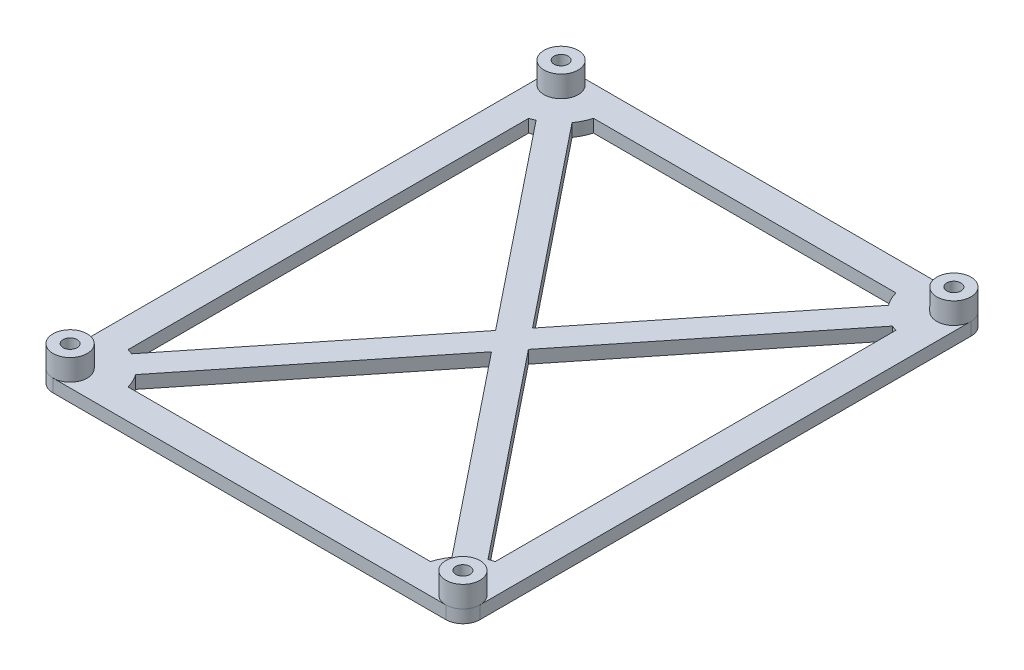
SolidWorks part; units mm, degrees
ref_plane "Front Plane" through (0, 0, 0) normal (0, 0, 1) x (1, 0, 0)
ref_plane "Top Plane" through (0, 0, 0) normal (0, 1, 0) x (1, 0, 0)
ref_plane "Right Plane" through (0, 0, 0) normal (1, 0, 0) x (0, 0, -1)
sketch "Sketch1" plane through (0, 0, 0) normal (0, 1, 0) x (1, 0, 0)
  line L1 (50, 61.5) -> (-50, 61.5)
  line L2 (50, 61.5) -> (50, -61.5)
  line L3 (50, -61.5) -> (-50, -61.5)
  line L4 (-50, 61.5) -> (-50, -61.5)
  line L5 (0, -61.5) -> (0, 61.5) construction
  line L6 (50, 0) -> (-50, 0) construction
  point P0 (0, 0)
  dimension "D1" = 123
  dimension "D2" = 100
extrude "Boss-Extrude1" add sketch "Sketch1" along normal blind 3
sketch "Sketch2" plane through (0, 3, 0) normal (0, 1, 0) x (1, 0, 0)
  line L0 (-46, 0) -> (0, 0) construction
  line L1 (-46, 57.5) -> (46, 57.5) construction
  line L2 (-46, 57.5) -> (-46, -57.5) construction
  line L3 (-46, -57.5) -> (46, -57.5) construction
  line L4 (46, 57.5) -> (46, -57.5) construction
  line L5 (0, 0) -> (0, 57.5) construction
  circle A1 centre (46, 57.5) radius 4
  circle A2 centre (46, -57.5) radius 4
  circle A3 centre (-46, -57.5) radius 4
  circle A4 centre (-46, 57.5) radius 4
  dimension "D1" = 8
  dimension "D2" = 92
  dimension "D3" = 115
extrude "Boss-Extrude2" add sketch "Sketch2" along normal blind 5
sketch "Sketch3" plane through (0, 3, 0) normal (0, 1, 0) x (1, 0, 0)
  line L8 (-43, 46.917) -> (-43, -46.917)
  line L9 (-43, 46.917) -> (-43, -46.917)
  line L10 (-35.417, -54.5) -> (35.417, -54.5)
  line L11 (-35.417, -54.5) -> (35.417, -54.5)
  line L16 (43, -46.917) -> (43, 46.917)
  line L17 (43, -46.917) -> (43, 46.917)
  line L18 (35.417, 54.5) -> (-35.417, 54.5)
  line L19 (35.417, 54.5) -> (-35.417, 54.5)
  arc A4 (-43, 46.917) -> (-35.417, 54.5) centre (-46, 57.5) ccw
  arc A6 (-43, 46.917) -> (-35.417, 54.5) centre (-46, 57.5) ccw
  arc A10 (-35.417, -54.5) -> (-43, -46.917) centre (-46, -57.5) ccw
  arc A13 (-35.417, -54.5) -> (-43, -46.917) centre (-46, -57.5) ccw
  arc A15 (43, -46.917) -> (35.417, -54.5) centre (46, -57.5) ccw
  arc A16 (43, -46.917) -> (35.417, -54.5) centre (46, -57.5) ccw
  arc A17 (35.417, 54.5) -> (43, 46.917) centre (46, 57.5) ccw
  arc A18 (35.417, 54.5) -> (43, 46.917) centre (46, 57.5) ccw
  dimension "D1" = 7
extrude "Cut-Extrude1" cut sketch "Sketch3" against normal through all
fillet "Fillet1" radius 4 4 edges at (-50, 1.5, -61.5) (50, 1.5, -61.5) (50, 1.5, 61.5) (-50, 1.5, 61.5)
sketch "Sketch4" plane through (0, 3, 0) normal (0, 1, 0) x (1, 0, 0)
  line L0 (-46, 57.5) -> (46, -57.5) construction
  line L1 (-46, -57.5) -> (46, 57.5) construction
  line L3 (-48.3426, 55.6259) -> (43.6574, -59.3741)
  line L4 (-43.6574, -59.3741) -> (48.3426, 55.6259)
  line L5 (-43.6574, 59.3741) -> (48.3426, -55.6259)
  line L6 (-48.3426, -55.6259) -> (43.6574, 59.3741)
  line L7 (-48.3426, 55.6259) -> (-43.6574, 59.3741)
  line L8 (43.6574, -59.3741) -> (48.3426, -55.6259)
  line L9 (-43.6574, -59.3741) -> (-48.3426, -55.6259)
  line L10 (48.3426, 55.6259) -> (43.6574, 59.3741)
  line L11 (-46, -57.5) -> (46, 57.5) construction
  line L13 (-46, 57.5) -> (46, -57.5) construction
  circle A0 centre (46, -57.5) radius 4 construction
  point P7 (-46, 57.5)
  point P17 (40.0223, 51.4818)
  point P20 (39.9854, 51.5119)
  point P21 (40, 51.5)
  point P22 (46, 57.5)
  point P23 (45.8888, -57.7707)
  point P24 (40, 51.5)
  point P25 (43, 50.342)
  point P26 (0, 0)
  point P31 (-46, -57.5)
  dimension "D1" = 3
  dimension "D2" = 3
extrude "Boss-Extrude3" add sketch "Sketch4" against normal through all
hole_wizard "M4x0.7 Tapped Hole1" positions "Sketch5" profile "Sketch6" tap size "M4x0.7" standard "ANSI Metric" end condition through all
sketch "Sketch5" plane through (0, 8, 0) normal (0, 1, 0) x (1, 0, 0)
  point P0 (-46, 57.5)
  point P3 (46, 57.5)
  point P6 (46, -57.5)
  point P9 (-46, -57.5)
sketch "Sketch6" plane through (-46, 8, -57.5) normal (1, 0, 0) x (0, 0, 1)
  line L0 (0, 0) -> (0, 8)
  line L1 (0, 8) -> (1.65, 8)
  line L2 (1.65, 8) -> (1.65, 0)
  line L5 (1.65, 0) -> (0, 0)
  line L11 (0, -6.35) -> (0, 107.95) construction
  dimension "Thru Tap Drill Dia." = 3.3
  dimension "Thru Tap Drill Depth" = 8
cosmetic thread "Hole Thread1" parameters "D2"=4
cosmetic thread "Hole Thread2" parameters "D2"=4
cosmetic thread "Hole Thread3" parameters "D2"=4
cosmetic thread "Hole Thread4" parameters "D2"=4
